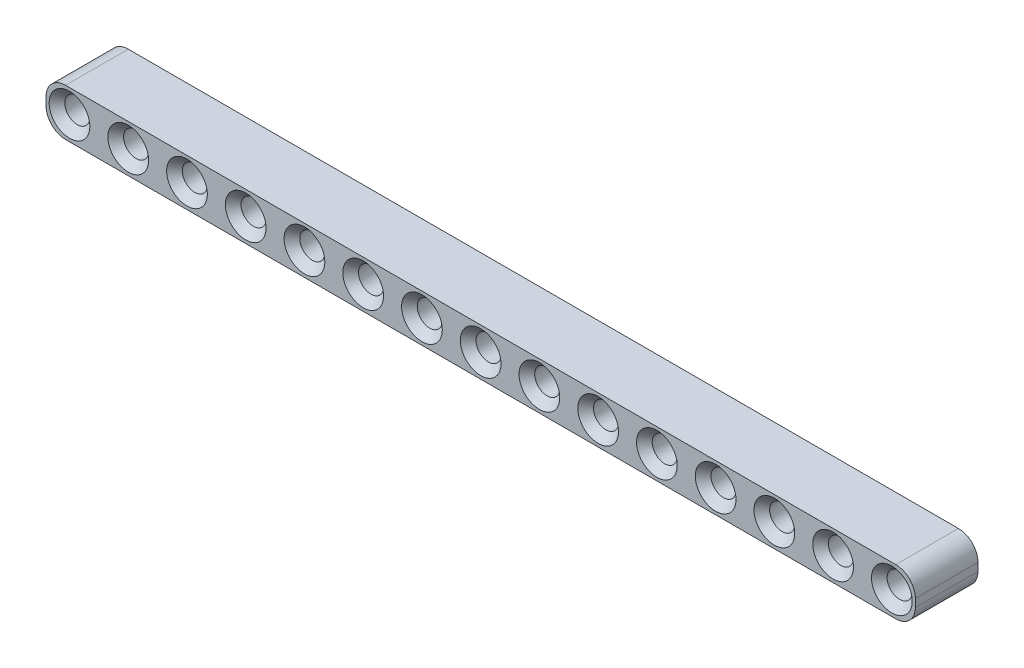
SolidWorks part; units mm, degrees
ref_plane "Front Plane" through (0, 0, 0) normal (0, 0, 1) x (1, 0, 0)
ref_plane "Top Plane" through (0, 0, 0) normal (0, 1, 0) x (1, 0, 0)
ref_plane "Right Plane" through (0, 0, 0) normal (1, 0, 0) x (0, 0, -1)
sketch "Sketch1" plane through (0, 0, 0) normal (0, 0, 1) x (1, 0, 0)
  line L1 (-0.5, 3) -> (105.5, 3)
  line L2 (-3, 0.5) -> (-3, -0.5)
  line L3 (-0.5, -3) -> (105.5, -3)
  line L4 (108, 0.5) -> (108, -0.5)
  circle A0 centre (0, 0) radius 1.6
  arc A1 (105.5, -3) -> (108, -0.5) centre (105.5, -0.5) ccw
  arc A2 (105.5, 3) -> (108, 0.5) centre (105.5, 0.5) cw
  arc A3 (-3, -0.5) -> (-0.5, -3) centre (-0.5, -0.5) ccw
  arc A4 (-0.5, 3) -> (-3, 0.5) centre (-0.5, 0.5) ccw
  circle A5 centre (7.5, 0) radius 1.6
  circle A6 centre (15, 0) radius 1.6
  circle A7 centre (22.5, 0) radius 1.6
  circle A8 centre (30, 0) radius 1.6
  circle A9 centre (37.5, 0) radius 1.6
  circle A10 centre (45, 0) radius 1.6
  circle A11 centre (52.5, 0) radius 1.6
  circle A12 centre (60, 0) radius 1.6
  circle A13 centre (67.5, 0) radius 1.6
  circle A14 centre (75, 0) radius 1.6
  circle A15 centre (82.5, 0) radius 1.6
  circle A16 centre (90, 0) radius 1.6
  circle A17 centre (97.5, 0) radius 1.6
  circle A18 centre (105, 0) radius 1.6
  point P8 (-3, 0)
  point P14 (-3, -3)
  point P17 (-3, 3)
  dimension "D1" = 3.2
  dimension "D4" = 2.5
  dimension "D2" = 6
  dimension "D3" = 3
  dimension "D6" = 7.5
  dimension "D5" = 15
extrude "Boss-Extrude1" add sketch "Sketch1" along normal blind 8
chamfer "Chamfer1" distance 1 angle 45 30 edges at (84.1, 0, 0) (84.1, 0, 8) (91.6, 0, 0) (91.6, 0, 8) (99.1, 0, 0) (99.1, 0, 8) (106.6, 0, 0) (106.6, 0, 8) (76.6, 0, 0) (76.6, 0, 8) (69.1, 0, 0) (69.1, 0, 8) (61.6, 0, 0) (61.6, 0, 8) (54.1, 0, 0) (54.1, 0, 8) (46.6, 0, 0) (46.6, 0, 8) (39.1, 0, 0) (39.1, 0, 8) (31.6, 0, 0) (31.6, 0, 8) (24.1, 0, 0) (24.1, 0, 8) (16.6, 0, 0) (16.6, 0, 8) (9.1, 0, 0) (9.1, 0, 8) (1.6, 0, 0) (1.6, 0, 8)
